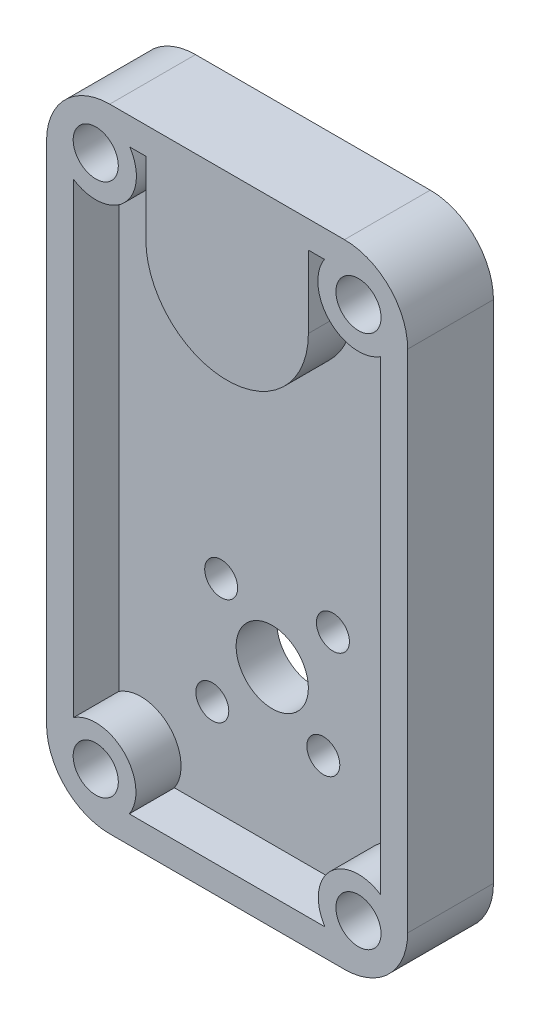
SolidWorks part; units mm, degrees
other "Camera1"
ref_plane "Front Plane" through (0, 0, 0) normal (0, 0, 1) x (1, 0, 0)
ref_plane "Top Plane" through (0, 0, 0) normal (0, 1, 0) x (1, 0, 0)
ref_plane "Right Plane" through (0, 0, 0) normal (1, 0, 0) x (0, 0, -1)
sketch "Sketch1" plane through (0, 0, 0) normal (0, 0, 1) x (1, 0, 0)
  line L0 (20, 0) -> (20, 70) construction
  line L1 (0, 0) -> (40, 0)
  line L2 (0, 0) -> (0, 70)
  line L3 (0, 70) -> (40, 70)
  line L4 (40, 0) -> (40, 70)
  line L5 (0, 20) -> (40, 20) construction
  line L6 (40, 0) -> (13.2825, 26.7175) construction
  line L7 (26.7175, 26.7175) -> (0, 0) construction
  circle A0 centre (20, 20) radius 9.5 construction
  circle A2 centre (25.6569, 14.3431) radius 1.825
  circle A4 centre (14.3431, 25.6569) radius 1.825
  circle A6 centre (20, 20) radius 4
  circle A7 centre (20, 20) radius 8 construction
  circle A8 centre (26.7175, 26.7175) radius 1.825
  circle A9 centre (13.3588, 13.3588) radius 1.825
  dimension "D4" = 19
  dimension "D5" = 3.65
  dimension "D6" = 8
  dimension "D7" = 16
  dimension "D1" = 70
  dimension "D2" = 40
  dimension "D3" = 20
extrude "Boss-Extrude1" add sketch "Sketch1" along normal blind 4.5
sketch "Sketch3" plane through (0, 0, 4.5) normal (0, 0, 1) x (1, 0, 0)
  line L0 (0, 0) -> (40, 0) construction
  line L1 (40, 0) -> (40, 70) construction
  line L2 (40, 70) -> (0, 70) construction
  line L3 (0, 70) -> (0, 0) construction
  line L4 (0, 0) -> (40, 0)
  line L5 (40, 0) -> (40, 70)
  line L6 (40, 70) -> (0, 70)
  line L7 (0, 70) -> (0, 0)
  line L8 (9.1648, 3) -> (30.8352, 3)
  line L9 (37, 9.1648) -> (37, 60.7754)
  line L10 (30.7754, 67) -> (29, 67)
  line L11 (3, 60.7754) -> (3, 9.1648)
  line L12 (20, 70) -> (20, 0) construction
  line L13 (3, 59) -> (37, 59) construction
  line L14 (11, 59) -> (11, 67)
  line L15 (29, 59) -> (29, 67)
  line L16 (11, 67) -> (9.2246, 67)
  line L17 (37, 67) -> (3, 67) construction
  line L18 (3, 67) -> (3, 3) construction
  line L19 (37, 3) -> (37, 67) construction
  line L20 (3, 3) -> (37, 3) construction
  circle A0 centre (20, 59) radius 7 construction
  arc A1 (11, 59) -> (29, 59) centre (20, 59) ccw
  circle A2 centre (20, 59) radius 9 construction
  circle A3 centre (5.45, 64.55) radius 2.45 construction
  arc A4 (3, 60.7754) -> (9.2246, 67) centre (5.45, 64.55) ccw
  arc A8 (9.1648, 3) -> (3, 9.1648) centre (5.45, 5.45) ccw
  arc A9 (30.8352, 3) -> (37, 9.1648) centre (34.55, 5.45) cw
  arc A10 (37, 60.7754) -> (30.7754, 67) centre (34.55, 64.55) cw
  dimension "D3" = 14
  dimension "D5" = 4.9
  dimension "D6" = 9
  dimension "D2" = 11
  dimension "D1" = 3
  dimension "D4" = 2
extrude "Boss-Extrude2" add sketch "Sketch3" along normal blind 5
sketch "Sketch6" plane through (0, 0, 9.5) normal (0, 0, 1) x (1, 0, 0)
  arc A0 (9.1648, 3) -> (3, 9.1648) centre (5.45, 5.45) ccw construction
  arc A1 (37, 9.1648) -> (30.8352, 3) centre (34.55, 5.45) ccw construction
  arc A2 (30.7754, 67) -> (37, 60.7754) centre (34.55, 64.55) ccw construction
  arc A3 (3, 60.7754) -> (9.2246, 67) centre (5.45, 64.55) ccw construction
  arc A4 (9.1648, 3) -> (3, 9.1648) centre (5.45, 5.45) ccw construction
  arc A5 (37, 9.1648) -> (30.8352, 3) centre (34.55, 5.45) ccw construction
  arc A6 (30.7754, 67) -> (37, 60.7754) centre (34.55, 64.55) ccw construction
  arc A7 (3, 60.7754) -> (9.2246, 67) centre (5.45, 64.55) ccw construction
  circle A8 centre (5.45, 64.55) radius 2.5
  circle A9 centre (5.45, 5.45) radius 2.5
  circle A10 centre (34.55, 5.45) radius 2.5
  circle A11 centre (34.55, 64.55) radius 2.5
  dimension "D1" = 5
extrude "Cut-Extrude3" cut sketch "Sketch6" against normal blind 7
ref_plane "Mid Plane - Length" through (20, 0, 0) normal (1, 0, 0) x (0, 0, -1)
ref_plane "Mid Plane - Width" through (0, 35, 0) normal (0, -1, 0) x (-1, 0, 0)
sketch "Sketch4" plane through (0, 0, 0) normal (0, 0, -1) x (-1, 0, 0)
  line L0 (-20, 70) -> (-20, 0) construction
  line L1 (-40, 70) -> (0, 70) construction
  line L2 (0, 0) -> (-40, 0) construction
  line L3 (-40, 66) -> (0, 66) construction
  line L4 (-40, 0) -> (-40, 70) construction
  line L5 (0, 70) -> (0, 0) construction
  line L6 (-40, 59) -> (0, 59) construction
  circle A0 centre (-20, 59) radius 7
  dimension "D3" = 14
  dimension "D1" = 4
  dimension "D2" = 7
extrude "Cut-Extrude1" cut sketch "Sketch4" against normal offset from surface (7.5 mm away) 2 up to face at (37.05, 64.55, 9.5)
sketch "Sketch5" plane through (0, 0, 0) normal (0, 0, -1) x (-1, 0, 0)
  line L0 (-20, 70) -> (-20, 39.0054) construction
  line L1 (-40, 70) -> (0, 70) construction
  arc A0 (-7.5811, 47.3088) -> (-32.9371, 47.0672) centre (-20, 20) ccw construction
  text T0 "4108" font "Century Gothic" height 6.25
  dimension "D1" = 50
extrude "Text-4108" [suppressed] cut sketch "Sketch5" against normal blind 1
fillet "Fillet1" radius 7 4 edges at (40, 70, 4.75) (0, 70, 4.75) (0, 0, 4.75) (40, 0, 4.75)
sketch "Sketch9" plane through (0, 0, 0) normal (0, 0, -1) x (-1, 0, 0)
  arc A0 (-6.2895, 46.6837) -> (-33.9585, 46.5549) centre (-20, 20) ccw construction
  text T0 "2208" font "Century Gothic" height 6
extrude "Text-2804" cut sketch "Sketch9" against normal blind 1
